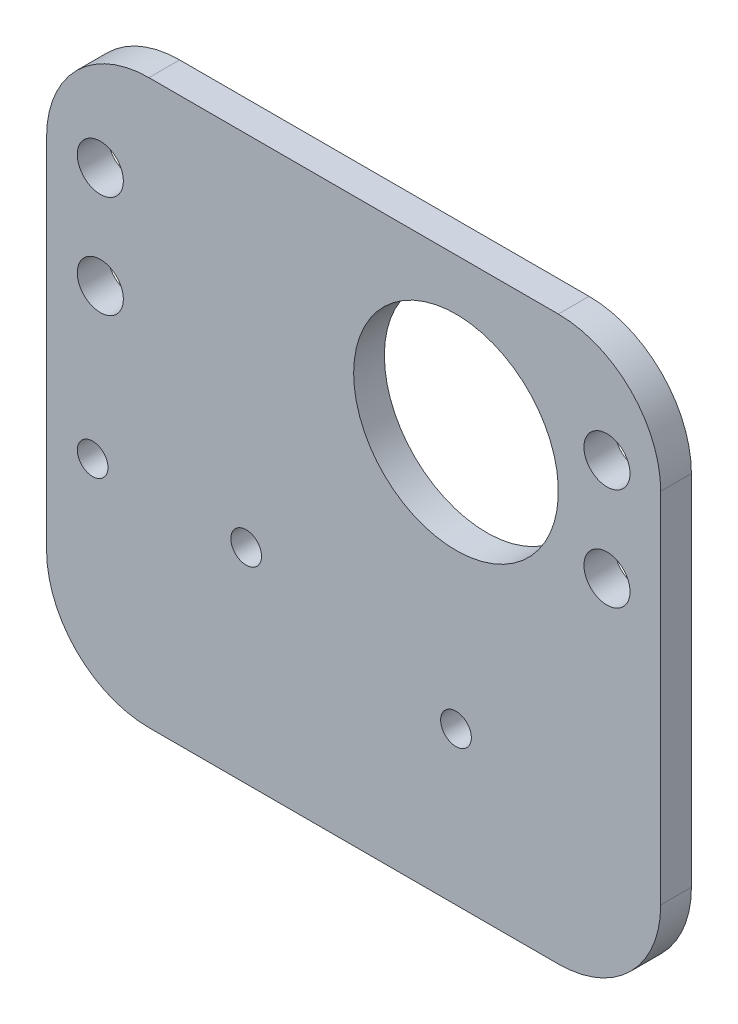
SolidWorks part; units mm, degrees
ref_plane "前视基准面" through (0, 0, 0) normal (0, 0, 1) x (1, 0, 0)
ref_plane "上视基准面" through (0, 0, 0) normal (0, 1, 0) x (1, 0, 0)
ref_plane "右视基准面" through (0, 0, 0) normal (1, 0, 0) x (0, 0, -1)
sketch "草图3" plane through (0, 0, 0) normal (0, 0, 1) x (1, 0, 0)
  line L0 (60.2665, 6.5325) -> (60.2665, 16.5325)
  line L1 (10.7665, 16.5325) -> (10.7665, 6.5325)
  line L2 (10.7665, 16.5325) -> (60.2665, 16.5325)
  circle A0 centre (60.2665, 16.5325) radius 3
  circle A1 centre (60.2665, 6.5325) radius 3
  circle A6 centre (10.7665, 6.5325) radius 3
  circle A7 centre (10.7665, 16.5325) radius 3
  dimension "D1" = 6
  dimension "D2" = 6
  dimension "D4" = 6
  dimension "D5" = 6
  dimension "D3" = 10
  dimension "D6" = 49.5
  dimension "D7" = 49.5
  dimension "D8" = 10
extrude "凸台-拉伸6" add sketch "草图3" along normal blind 0.001 contours A6 | A0 | A1 | A7
sketch "草图11" plane through (0, 0, 0.001) normal (0, 0, 1) x (1, 0, 0)
  circle A0 centre (10.7665, 16.5325) radius 2.25
  circle A1 centre (10.7665, 6.5325) radius 2.25
  circle A2 centre (60.2665, 16.5325) radius 2.25
  circle A3 centre (60.2665, 6.5325) radius 2.25
  dimension "D1" = 4.5
  dimension "D2" = 4.5
  dimension "D3" = 4.5
  dimension "D4" = 4.5
extrude "切除-拉伸2" cut sketch "草图11" against normal through all both and the other way through all
sketch "草图12" plane through (0, 0, 0.001) normal (0, 0, 1) x (1, 0, 0)
  line L4 (10.7665, 16.5325) -> (60.2665, 6.5325) construction
  line L5 (10.7665, 6.5325) -> (60.2665, 16.5325) construction
  line L6 (60.2665, 16.5325) -> (60.2665, 6.5325) construction
  line L7 (5.5165, 26.5325) -> (65.5165, 26.5325)
  line L8 (5.5165, 26.5325) -> (5.5165, 1.5325)
  line L9 (5.5165, -28.4675) -> (65.5165, -28.4675)
  line L10 (65.5165, 26.5325) -> (65.5165, -28.4675)
  line L11 (5.5165, 1.5325) -> (5.5165, -28.4675) construction
  line L13 (5.5165, -28.4675) -> (5.5165, 1.5325) construction
  line L16 (5.5165, 1.5325) -> (5.5165, -28.4675)
  circle A4 centre (45.5165, 11.5325) radius 10
  point P8 (35.5165, 11.5325)
  point P9 (35.5165, 26.5325)
  point P10 (-46.6091, 14.6442)
  point P11 (60.2665, 11.5325)
  dimension "D5" = 20
  dimension "D1" = 60
  dimension "D2" = 55
  dimension "D3" = 15
  dimension "D4" = 14.75
extrude "凸台-拉伸7" add sketch "草图12" along normal blind 3 contours L7 L10 L9 L16 L8
sketch "草图14" plane through (0, 0, 0.001) normal (0, 0, -1) x (-1, 0, 0)
  line L0 (-60.2665, 16.5325) -> (-60.2665, 6.5325) construction
  circle A0 centre (-60.2665, 6.5325) radius 2.25 construction
  circle A1 centre (-60.2665, 6.5325) radius 2.25
  circle A2 centre (-60.2665, 16.5325) radius 2.25 construction
  circle A3 centre (-60.2665, 16.5325) radius 2.25
  circle A4 centre (-10.7665, 6.5325) radius 2.25 construction
  circle A5 centre (-10.7665, 16.5325) radius 2.25 construction
  circle A6 centre (-10.7665, 6.5325) radius 2.25
  circle A7 centre (-10.7665, 16.5325) radius 2.25
  circle A8 centre (-45.5165, 11.5325) radius 10
  point P14 (-60.2665, 11.5325)
  point P15 (0.1696, -0.033)
  dimension "D2" = 20
  dimension "D1" = 14.75
extrude "切除-拉伸3" cut sketch "草图14" against normal blind 3
sketch "草图15" plane through (0, 0, 0.001) normal (0, 0, -1) x (-1, 0, 0)
  circle A0 centre (-45.5165, 11.5325) radius 10 construction
  circle A1 centre (-45.5165, 11.5325) radius 10
  circle A2 centre (-45.5165, -13.5675) radius 1.5
  dimension "D2" = 3
  dimension "D1" = 25.1
extrude "切除-拉伸4" cut sketch "草图15" against normal blind 3
sketch "草图16" plane through (0, 0, 3.001) normal (0, 0, 1) x (1, 0, 0)
  line L6 (5.5165, 26.5325) -> (5.5165, -28.4675) construction
  line L7 (5.5165, -28.4675) -> (65.5165, -28.4675) construction
  circle A0 centre (10.0165, -8.4675) radius 1.5
  circle A1 centre (25.0165, -8.4675) radius 1.5
  dimension "D1" = 3
  dimension "D2" = 4.5
  dimension "D3" = 20
  dimension "D5" = 15
  dimension "D4" = 2
extrude "切除-拉伸5" cut sketch "草图16" against normal blind 10
sketch "草图17" plane through (0, 0, 3.001) normal (0, 0, 1) x (1, 0, 0)
  circle A0 centre (45.5165, -13.5675) radius 7.5
  circle A1 centre (45.5165, -13.5675) radius 5.5
  dimension "D1" = 15
  dimension "D2" = 2
extrude "凸台-拉伸8" add sketch "草图17" against normal blind 7
fillet "圆角1" radius 10 4 edges at (65.5165, 26.5325, 1.501) (65.5165, -28.4675, 1.501) (5.5165, -28.4675, 1.501) (5.5165, 26.5325, 1.501)
